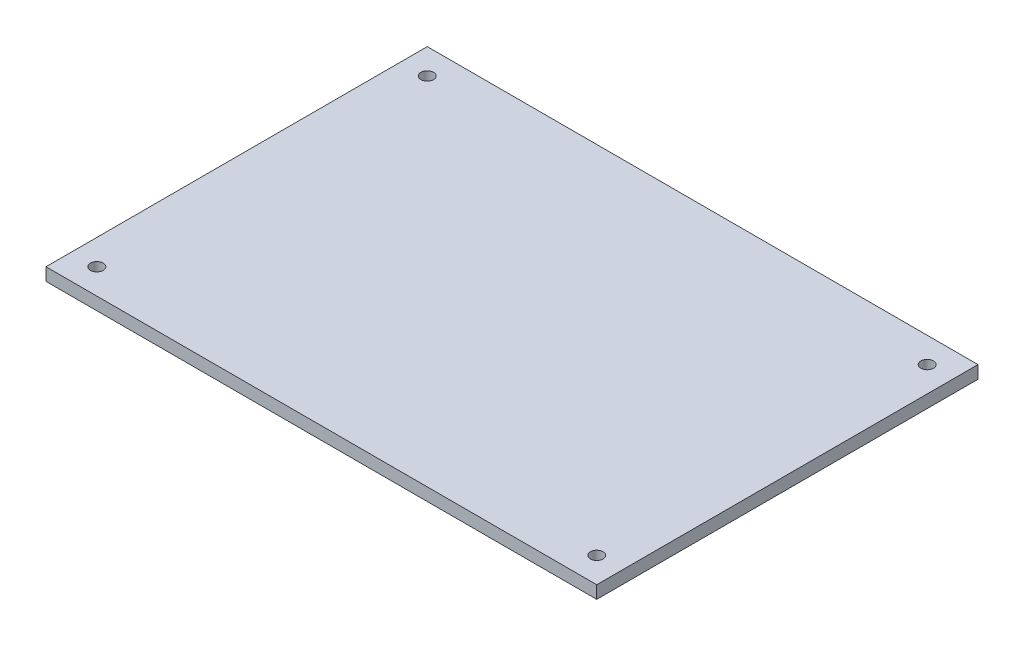
SolidWorks part; units mm, degrees
ref_plane "Front Plane" through (0, 0, 0) normal (0, 0, 1) x (1, 0, 0)
ref_plane "Top Plane" through (0, 0, 0) normal (0, 1, 0) x (1, 0, 0)
ref_plane "Right Plane" through (0, 0, 0) normal (1, 0, 0) x (0, 0, -1)
sketch "Sketch2" plane through (0, 0, 0) normal (0, 1, 0) x (1, 0, 0)
  line L1 (65, -45) -> (-65, -45)
  line L2 (65, -45) -> (65, 45)
  line L3 (65, 45) -> (-65, 45)
  line L4 (-65, -45) -> (-65, 45)
  line L5 (65, -45) -> (-65, 45) construction
  line L6 (65, 45) -> (-65, -45) construction
  point P0 (0, 0)
  dimension "D1" = 90
  dimension "D2" = 130
extrude "Boss-Extrude1" add sketch "Sketch2" along normal blind 3
sketch "Sketch3" plane through (0, 3, 0) normal (0, 1, 0) x (1, 0, 0)
  line L0 (-65, -45) -> (65, -45) construction
  line L1 (65, -45) -> (65, 45) construction
  circle A0 centre (59, -39) radius 1.5
  dimension "D1" = 3
  dimension "D2" = 6
  dimension "D3" = 6
extrude "Cut-Extrude1" cut sketch "Sketch3" against normal through all
pattern_linear "LPattern1" count 2 spacing 78 along (0, 0, -1) count 2 spacing 118 along (-1, 0, 0) of "Cut-Extrude1"
sketch "Sketch4" plane through (0, 3, 0) normal (0, 1, 0) x (1, 0, 0)
  line L0 (-59, 32.5) -> (-59, 21.0204)
  line L1 (-59, 21.0204) -> (-46.9733, 21.0204)
  line L2 (-52.5, 39) -> (-36.2345, 39)
  line L3 (-36.2345, 39) -> (-36.2345, 26.3365)
  line L4 (-52.5, -39) -> (-39.9482, -39)
  line L5 (-65, -45) -> (65, -45) construction
  line L8 (65, 45) -> (-65, 45) construction
  line L9 (-65, 45) -> (-65, -45) construction
  line L10 (-59, -32.5) -> (-59, -19.7433)
  line L11 (52.5, 39) -> (26.6274, 39)
  line L12 (59, 32.5) -> (59, 12.3765)
  line L14 (65, -45) -> (65, 45) construction
  line L15 (52.5, -39) -> (33.2697, -39)
  line L16 (59, -32.5) -> (59, -18.2504)
  arc A1 (-52.5, 39) -> (-59, 32.5) centre (-59, 39) cw
  arc A5 (-52.5, -39) -> (-59, -32.5) centre (-59, -39) ccw
  arc A6 (52.5, -39) -> (59, -32.5) centre (59, -39) cw
  arc A7 (59, 32.5) -> (52.5, 39) centre (59, 39) cw
  point P1 (0, 0)
  point P16 (-54.4038, -34.4038)
  point P32 (0, 0)
  point P37 (0, 0)
  point P39 (-54.4038, 34.4038)
  dimension "D1" = 6.5
  dimension "D2" = 6.5
